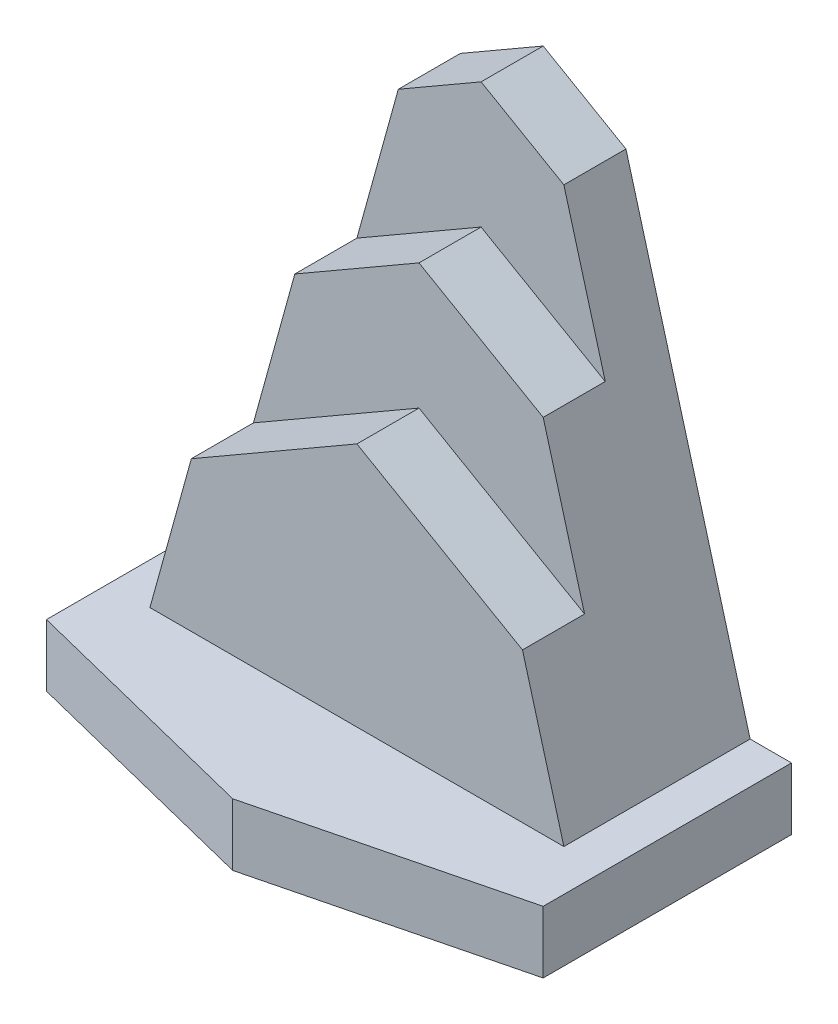
SolidWorks part; units mm, degrees
other "Perspective"
ref_plane "Front Plane" through (0, 0, 0) normal (0, 0, 1) x (1, 0, 0)
ref_plane "Top Plane" through (0, 0, 0) normal (0, 1, 0) x (1, 0, 0)
ref_plane "Right Plane" through (0, 0, 0) normal (1, 0, 0) x (0, 0, -1)
sketch "Sketch1" plane through (0, 0, 0) normal (0, 1, 0) x (1, 0, 0)
  line L0 (0, 0) -> (-60, -15)
  line L1 (-60, -15) -> (-120, 0)
  line L2 (-120, 0) -> (-120, 60)
  line L3 (-120, 60) -> (0, 60)
  line L4 (0, 60) -> (0, 0)
  line L5 (-60, -15) -> (-60, 60) construction
  dimension "D1" = 15
  dimension "D2" = 60
  dimension "D3" = 60
  dimension "D4" = 60
extrude "Extrude1" add sketch "Sketch1" along normal blind 15
sketch "Sketch2" plane through (0, 0, -60) normal (0, 0, -1) x (-1, 0, 0)
  line L0 (110, 15) -> (80, 123.453)
  line L1 (0, 15) -> (120, 15) construction
  line L2 (80, 123.453) -> (60, 135)
  line L3 (60, 135) -> (40, 123.453)
  line L4 (40, 123.453) -> (10, 15)
  line L5 (60, 15) -> (60, 135) construction
  line L10 (0, 0) -> (120, 0)
  line L11 (120, 0) -> (120, 15)
  line L12 (120, 15) -> (0, 15)
  line L13 (0, 15) -> (0, 0)
  line L16 (110, 15) -> (10, 15)
  dimension "D1" = 120
  dimension "D2" = 120
  dimension "D3" = 50
  dimension "D4" = 50
  dimension "D5" = 120
  dimension "D6" = 20
  dimension "D7" = 20
  dimension "D8" = 0
extrude "Extrude2" add sketch "Sketch2" against normal blind 15
sketch "Sketch3" plane through (0, 0, -45) normal (0, 0, 1) x (1, 0, 0)
  line L0 (-40, 123.453) -> (-10, 15)
  line L2 (-90, 87.302) -> (-60, 104.6225)
  line L3 (-60, 104.6225) -> (-30, 87.302)
  line L4 (-80, 123.453) -> (-110, 15)
  line L6 (-10, 15) -> (-110, 15)
  line L9 (-80, 123.453) -> (-60, 135) construction
  line L10 (-60, 135) -> (-40, 123.453) construction
  line M1 (-110, 15) -> (-10, 15)
  line M2 (-10, 15) -> (-40, 123.453)
  line M5 (-80, 123.453) -> (-110, 15)
  dimension "D1" = 10
  dimension "D2" = 10
extrude "Extrude3" add sketch "Sketch3" along normal blind 15 contours L3 L2 M5 M1 M2
sketch "Sketch4" plane through (0, 0, -30) normal (0, 0, 1) x (1, 0, 0)
  line L0 (-110, 15) -> (-10, 15)
  line L1 (-10, 15) -> (-20, 51.151)
  line L2 (-10, 15) -> (-30, 87.302) construction
  line L3 (-20, 51.151) -> (-60, 74.245)
  line L4 (-60, 74.245) -> (-100, 51.151)
  line L5 (-90, 87.302) -> (-110, 15) construction
  line L6 (-100, 51.151) -> (-110, 15)
  line L7 (-60, 104.6225) -> (-30, 87.302) construction
  line L8 (-90, 87.302) -> (-60, 104.6225) construction
  dimension "D1" = 10
  dimension "D2" = 10
extrude "Extrude4" add sketch "Sketch4" along normal blind 15
